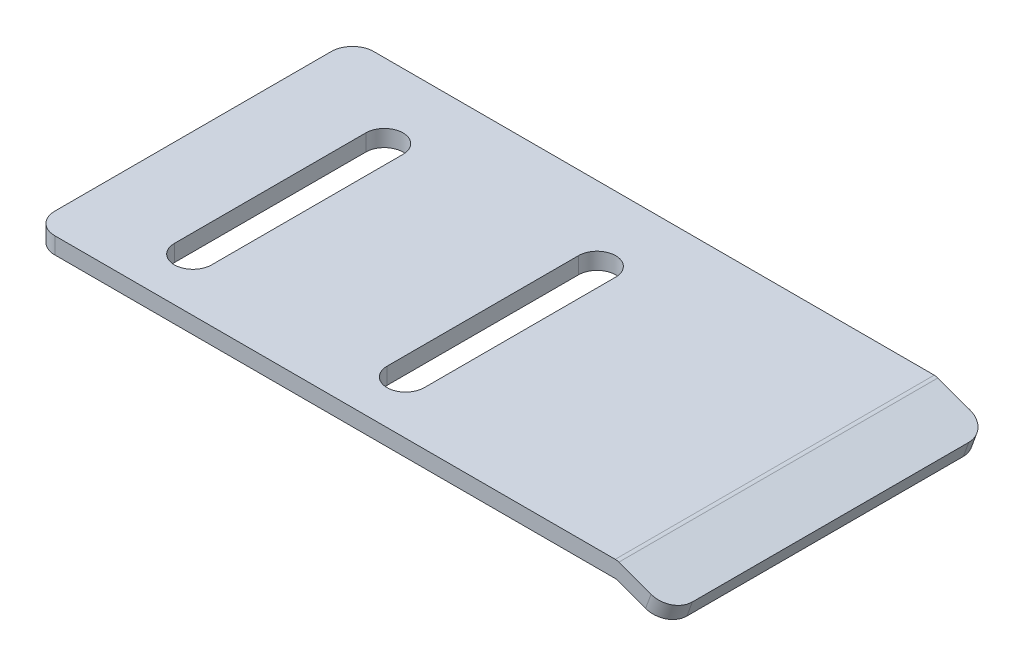
SolidWorks part; units mm, degrees
ref_plane "Front Plane" through (0, 0, 0) normal (0, 0, 1) x (1, 0, 0)
ref_plane "Top Plane" through (0, 0, 0) normal (0, 1, 0) x (1, 0, 0)
ref_plane "Right Plane" through (0, 0, 0) normal (1, 0, 0) x (0, 0, -1)
sketch "Sketch1" plane through (0, 0, 0) normal (0, 0, 1) x (1, 0, 0)
  line L0 (-37.5773, 8.5792) -> (17.3083, 8.5792)
  line L1 (17.3083, 8.5792) -> (22.3827, 6.7323)
  line L2 (22.3827, 6.7323) -> (21.8696, 5.3228)
  line L3 (21.8696, 5.3228) -> (17.2227, 7.0141)
  line L4 (17.2227, 7.0141) -> (-37.5773, 7.0141)
  line L5 (-37.5773, 7.0141) -> (-37.5773, 8.5792)
  dimension "D1" = 5.4
  dimension "D2" = 20
  dimension "D3" = 54.8
  dimension "D4" = 1.5
  dimension "D5" = 59.96
extrude "Boss-Extrude1" add sketch "Sketch1" along normal blind 30
fillet "Fillet1" radius 1 1 edges at (17.3083, 8.5792, 15)
fillet "Fillet2" radius 2 4 edges at (-37.5773, 7.7967, 30) (-37.5773, 7.7967, 0) (22.1261, 6.0276, 30) (22.1261, 6.0276, 0)
sketch "Sketch3" plane through (0, 8.5792, 0) normal (0, 1, 0) x (1, 0, 0)
  line L2 (-25.8273, -25) -> (-25.8273, -7)
  line L4 (-29.3273, -25) -> (-29.3273, -7)
  line L6 (-5.8273, -25) -> (-5.8273, -7)
  line L8 (-9.3273, -25) -> (-9.3273, -7)
  arc A0 (-5.8273, -7) -> (-9.3273, -7) centre (-7.5773, -7) ccw
  arc A1 (-9.3273, -25) -> (-5.8273, -25) centre (-7.5773, -25) ccw
  arc A2 (-29.3273, -25) -> (-25.8273, -25) centre (-27.5773, -25) ccw
  arc A3 (-25.8273, -7) -> (-29.3273, -7) centre (-27.5773, -7) ccw
  dimension "D1" = 3.5
  dimension "D2" = 18
extrude "Cut-Extrude1" cut sketch "Sketch3" against normal through all
